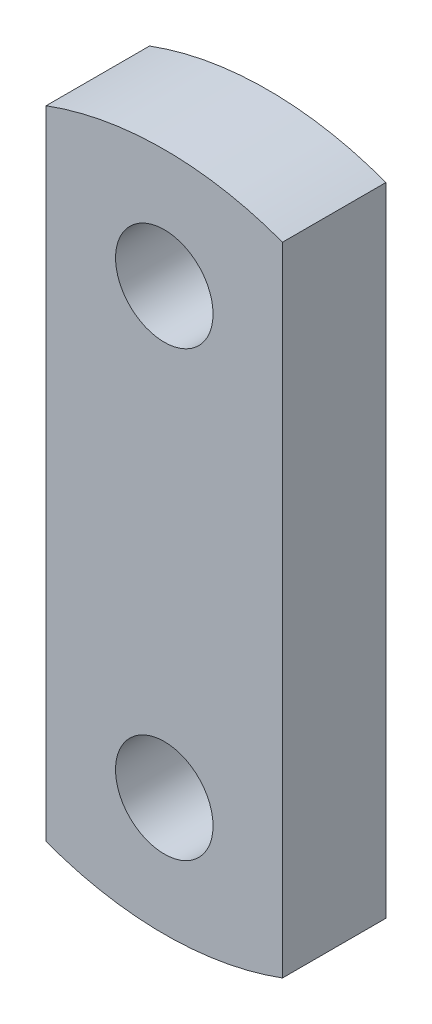
SolidWorks part; units mm, degrees
ref_plane "Front Plane" through (0, 0, 0) normal (0, 0, 1) x (1, 0, 0)
ref_plane "Top Plane" through (0, 0, 0) normal (0, 1, 0) x (1, 0, 0)
ref_plane "Right Plane" through (0, 0, 0) normal (1, 0, 0) x (0, 0, -1)
sketch "Sketch1" plane through (0, 0, 0) normal (0, 0, 1) x (1, 0, 0)
  line L2 (-57.3726, 131.4782) -> (-57.3726, -84.1604)
  line L3 (-137.3726, 131.4782) -> (-137.3726, -84.1604)
  circle A0 centre (-97.3726, 98.6589) radius 16.5
  circle A1 centre (-97.3726, -51.3411) radius 16.5
  arc A2 (-137.3726, -84.1604) -> (-57.3726, -84.1604) centre (-97.3726, 23.6589) ccw
  arc A3 (-57.3726, 131.4782) -> (-137.3726, 131.4782) centre (-97.3726, 23.6589) ccw
  point P3 (-97.3726, 23.6589)
  point P10 (-97.3726, 23.6589)
  point P13 (-57.3726, 23.6589)
  point P16 (-137.3726, 23.6589)
extrude "Boss-Extrude1" add sketch "Sketch1" along normal blind 35
